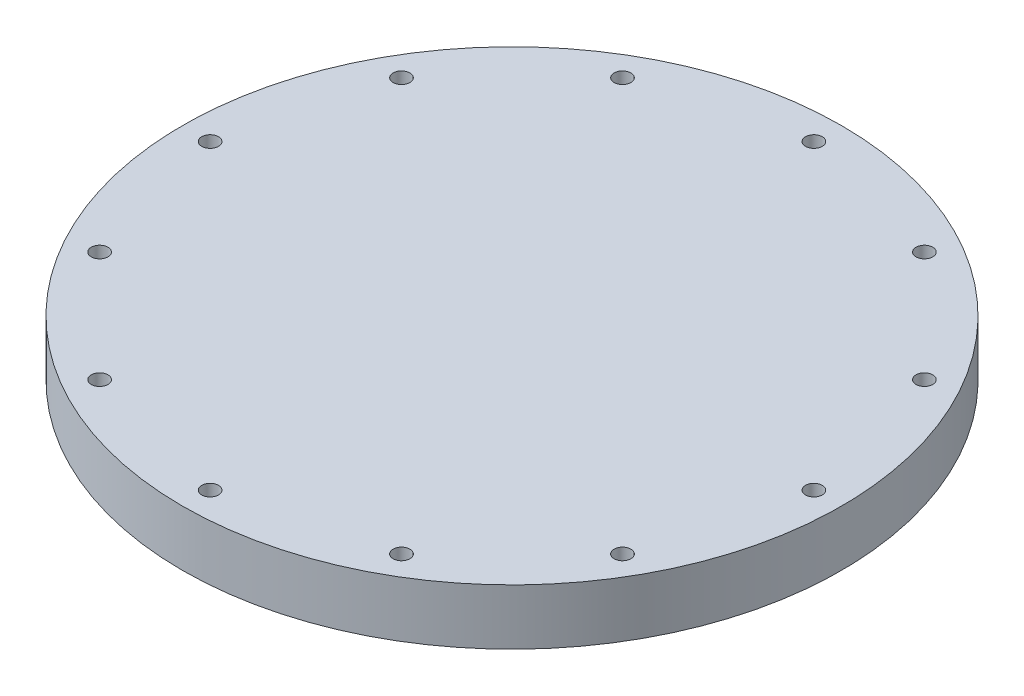
SolidWorks part; units mm, degrees
material "7075-T6 (SN)"
ref_plane "Front Plane" through (0, 0, 0) normal (0, 0, 1) x (1, 0, 0)
ref_plane "Top Plane" through (0, 0, 0) normal (0, 1, 0) x (1, 0, 0)
ref_plane "Right Plane" through (0, 0, 0) normal (1, 0, 0) x (0, 0, -1)
sketch "Sketch2" plane through (0, 0, 0) normal (0, 1, 0) x (1, 0, 0)
  circle A1 centre (0, 0) radius 25.4
  dimension "D1" = 50.8
extrude "Base Cylinder" add sketch "Sketch2" along normal blind 19.05
sketch "Sketch3" plane through (0, 0, 0) normal (0, -1, 0) x (1, 0, 0)
  circle A1 centre (0, 0) radius 56.3562
  dimension "D1" = 112.7125
extrude "Aft Flange" add sketch "Sketch3" against normal blind 9.525
sketch "Sketch For Bolt Holes" plane through (0, 0, 0) normal (0, -1, 0) x (1, 0, 0)
  circle A0 centre (-51.6255, 0) radius 1.5875
  circle A1 centre (-44.709, 25.8128) radius 1.5875
  circle A2 centre (-25.8128, 44.709) radius 1.5875
  circle A3 centre (0, 51.6255) radius 1.5875
  circle A4 centre (25.8127, 44.709) radius 1.5875
  circle A5 centre (44.709, 25.8128) radius 1.5875
  circle A6 centre (51.6255, 0) radius 1.5875
  circle A7 centre (44.709, -25.8127) radius 1.5875
  circle A8 centre (25.8128, -44.709) radius 1.5875
  circle A9 centre (0, -51.6255) radius 1.5875
  circle A10 centre (-25.8127, -44.709) radius 1.5875
  circle A11 centre (-44.709, -25.8128) radius 1.5875
  point P36 (0, 0)
  dimension "D2" = 3.175
  dimension "D1" = 51.6255
  dimension "D3" = 12
hole_wizard "Bolt Circle" positions "Sketch8" profile "Sketch9" hole size "#4-40" standard "ANSI Inch" end condition up to next
sketch "Sketch8" plane through (0, 0, 0) normal (0, -1, 0) x (-1, 0, 0)
  point P0 (-25.8127, -44.709)
  point P3 (-44.709, -25.8128)
  point P6 (-51.6255, 0)
  point P9 (-44.709, 25.8127)
  point P12 (-25.8128, 44.709)
  point P15 (0, 51.6255)
  point P18 (25.8127, 44.709)
  point P21 (44.709, 25.8128)
  point P24 (51.6255, 0)
  point P27 (44.709, -25.8128)
  point P30 (25.8128, -44.709)
  point P33 (0, -51.6255)
  point P36 (-25.8127, -44.709)
  point P38 (-44.709, -25.8128)
  point P40 (-51.6255, 0)
sketch "Sketch9" plane through (25.8127, 0, 44.709) normal (1, 0, 0) x (0, 0, -1)
  line L0 (0, 0) -> (0, 9.525)
  line L1 (0, 9.525) -> (1.4351, 9.525)
  line L2 (1.4351, 9.525) -> (1.4351, 0)
  line L5 (1.4351, 0) -> (0, 0)
  line L11 (0, -6.35) -> (0, 107.95) construction
  dimension "Thru Hole Dia." = 2.8702
  dimension "Thru Hole Depth" = 9.525
sketch "Sketch20" plane through (0, 0, 0) normal (0, 0, 1) x (1, 0, 0)
  line L0 (56.3562, 9.525) -> (-56.3562, 9.525) construction
  line L1 (-39.6604, 25.9889) -> (32.2639, 25.9889)
  line L2 (-39.6604, 25.9889) -> (-39.6604, 9.525)
  line L3 (-39.6604, 9.525) -> (32.2639, 9.525)
  line L4 (32.2639, 25.9889) -> (32.2639, 9.525)
extrude "Cut-Extrude2" cut sketch "Sketch20" against normal mid plane 304.8
